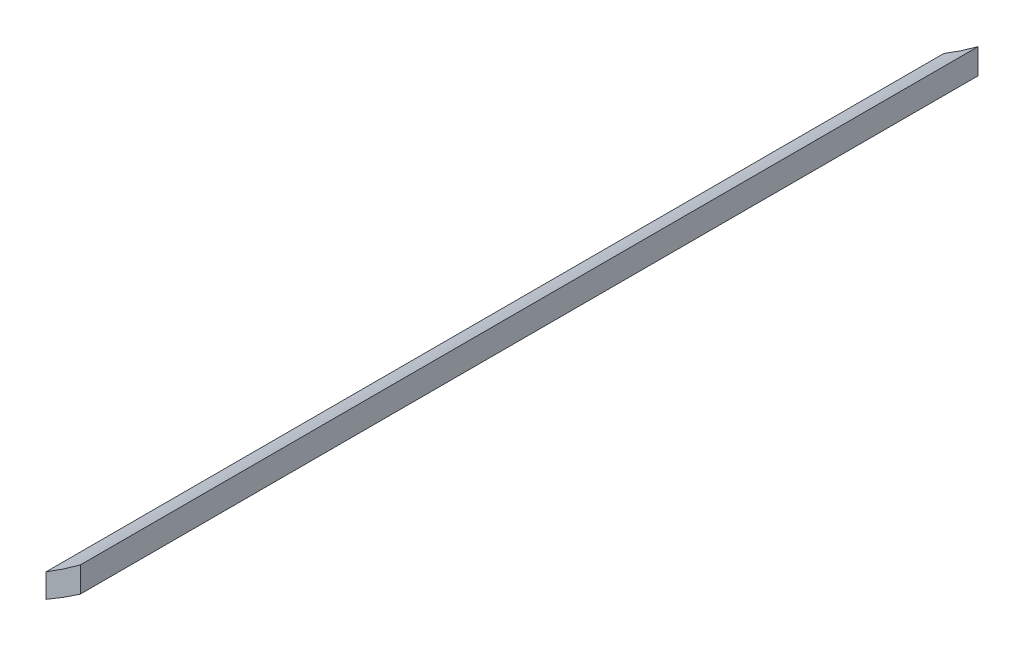
SolidWorks part; units mm, degrees
ref_plane "Front Plane" through (0, 0, 0) normal (0, 0, 1) x (1, 0, 0)
ref_plane "Top Plane" through (0, 0, 0) normal (0, 1, 0) x (1, 0, 0)
ref_plane "Right Plane" through (0, 0, 0) normal (1, 0, 0) x (0, 0, -1)
sketch "Sketch1" plane through (0, 0, 0) normal (0, 0, 1) x (1, 0, 0)
  line L16 (124.2584, -49.2067) -> (124.2584, -50.7562)
  line L17 (122.1584, -50.622) -> (122.1584, -52.0819)
  spline S12 degree 3 poles (122.1584, -52.0819) (122.4669, -51.9079) (122.7713, -51.7268) (123.4736, -51.2889) (123.8689, -51.0271) (124.2584, -50.7562) knots 0.649205 0.649205 0.649205 0.649205 0.75 0.75 0.885223 0.885223 0.885223 0.885223
  spline S13 degree 3 poles (124.2584, -49.2067) (123.8646, -49.4968) (123.465, -49.7784) (122.7623, -50.2463) (122.4626, -50.4375) (122.1584, -50.622) knots 0.114062 0.114062 0.114062 0.114062 0.25 0.25 0.348788 0.348788 0.348788 0.348788
extrude "Boss-Extrude1" add sketch "Sketch1" along normal blind 55
